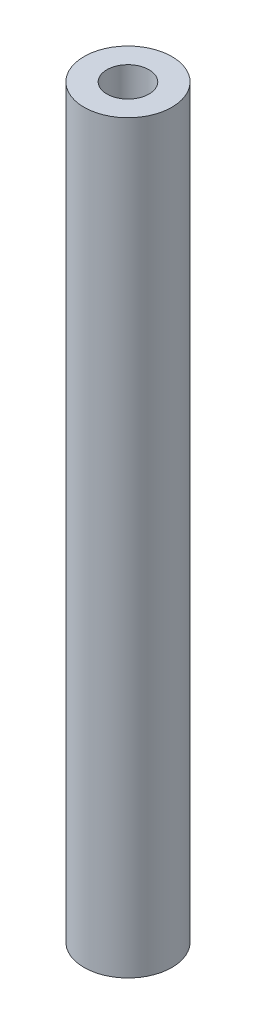
SolidWorks part; units mm, degrees
material "AISI Type 316L stainless steel"
ref_plane "Front Plane" through (0, 0, 0) normal (0, 0, 1) x (1, 0, 0)
ref_plane "Top Plane" through (0, 0, 0) normal (0, 1, 0) x (1, 0, 0)
ref_plane "Right Plane" through (0, 0, 0) normal (1, 0, 0) x (0, 0, -1)
sketch "Sketch1" plane through (0, 0, 0) normal (0, 1, 0) x (1, 0, 0)
  circle A0 centre (0, 0) radius 3.175
  circle A1 centre (0, 0) radius 1.524
  dimension "D1" = 6.35
  dimension "D2" = 3.048
extrude "Boss-Extrude1" add sketch "Sketch1" along normal blind 53.834
